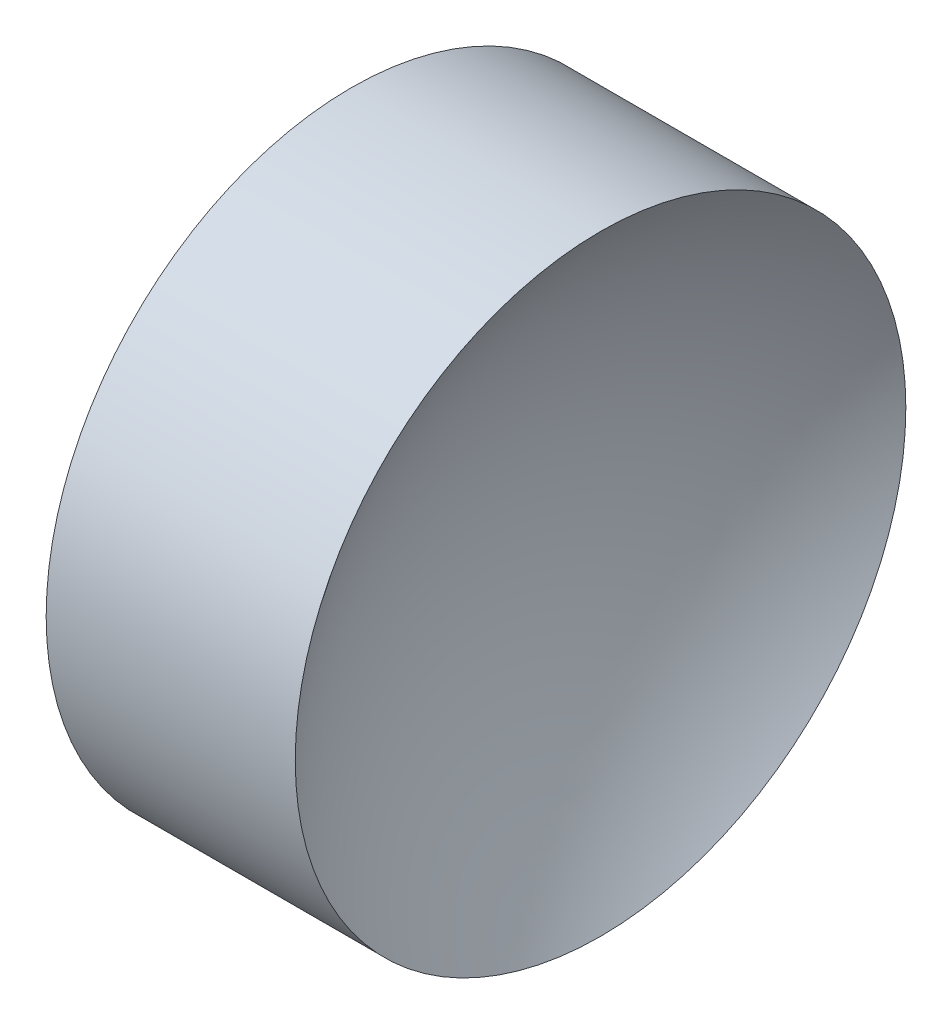
SolidWorks part; units mm, degrees
ref_plane "前视基准面" through (0, 0, 0) normal (0, 0, 1) x (1, 0, 0)
ref_plane "上视基准面" through (0, 0, 0) normal (0, 1, 0) x (1, 0, 0)
ref_plane "右视基准面" through (0, 0, 0) normal (1, 0, 0) x (0, 0, -1)
sketch "草图1" plane through (0, 0, 0) normal (0, 0, 1) x (1, 0, 0)
  line L0 (21.2249, 13.0445) -> (26.692, 13.0445) construction
  line L1 (22.1722, 13.0445) -> (22.1722, 16.1945)
  line L2 (23.6722, 13.0445) -> (22.1722, 13.0445)
  line L3 (22.1722, 16.1945) -> (24.7422, 16.1945)
  arc A0 (24.7422, 16.1945) -> (23.6722, 13.0445) centre (28.8438, 13.0445) ccw
revolve "旋转1" add sketch "草图1" angle 360 about L0
